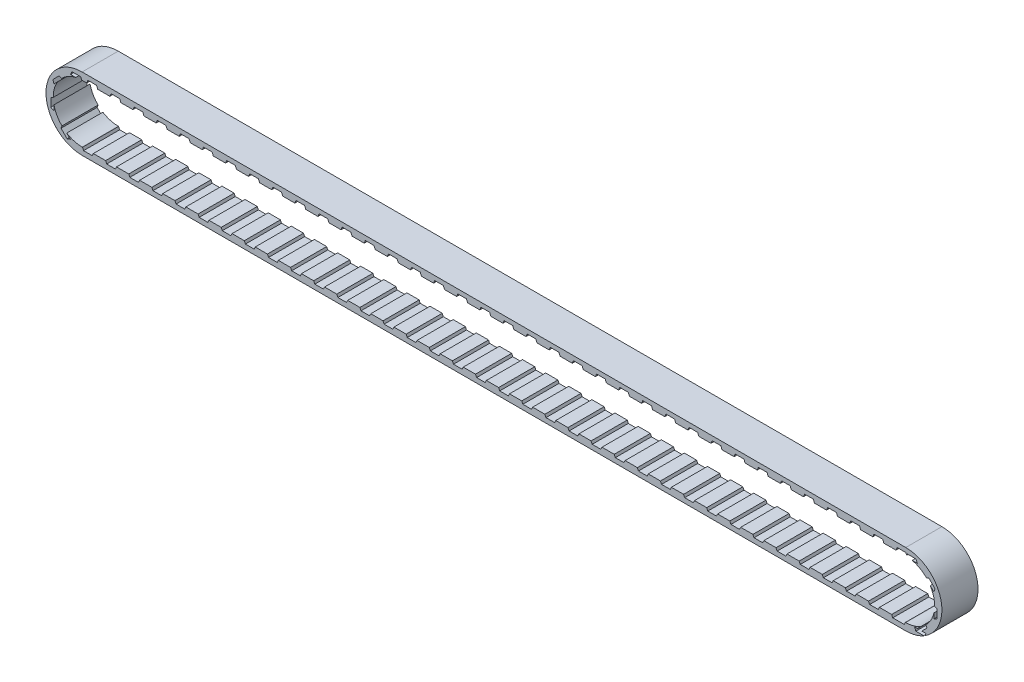
SolidWorks part; units mm, degrees
ref_plane "Front Plane" through (0, 0, 0) normal (0, 0, 1) x (1, 0, 0)
ref_plane "Top Plane" through (0, 0, 0) normal (0, 1, 0) x (1, 0, 0)
ref_plane "Right Plane" through (0, 0, 0) normal (1, 0, 0) x (0, 0, -1)
sketch "Sketch1" plane through (0, 0, 0) normal (0, 0, 1) x (1, 0, 0)
  line L1 (-72.39, 6.35) -> (72.39, 6.35)
  line L2 (-72.39, 5.08) -> (72.39, 5.08)
  line L3 (-72.39, -6.35) -> (72.39, -6.35)
  line L5 (-72.39, 6.35) -> (72.39, -6.35) construction
  line L6 (-72.39, -6.35) -> (72.39, 6.35) construction
  line L7 (-72.39, -5.08) -> (72.39, -5.08)
  line L9 (-72.39, 5.08) -> (72.39, -5.08) construction
  line L10 (-72.39, -5.08) -> (72.39, 5.08) construction
  arc A0 (-72.39, 6.35) -> (-72.39, -6.35) centre (-72.39, 0) ccw
  arc A1 (72.39, 6.35) -> (72.39, -6.35) centre (72.39, 0) cw
  arc A2 (-72.39, 5.08) -> (-72.39, -5.08) centre (-72.39, 0) ccw
  arc A3 (72.39, 5.08) -> (72.39, -5.08) centre (72.39, 0) cw
  point P0 (0, 0)
  point P8 (0, 0)
  point P15 (-78.74, 0)
  point P16 (78.74, 0)
  dimension "D2" = 6.35
  dimension "D4" = 144.78
  dimension "D1" = 144.78
  dimension "D3" = 1.27
  dimension "D5" = 144.78
extrude "Boss-Extrude1" add sketch "Sketch1" against normal blind 6.35
sketch "Sketch2" plane through (0, 0, 0) normal (0, 0, 1) x (1, 0, 0)
  line L0 (-72.39, -4.953) -> (-70.358, -4.953)
  line L3 (-70.358, -4.953) -> (-70.612, -5.5007)
  line L4 (-70.612, -5.5007) -> (-72.136, -5.5007)
  line L6 (-72.136, -5.5007) -> (-72.39, -4.953)
  line L7 (-72.39, -5.08) -> (72.39, -5.08) construction
  dimension "D1" = 0.127
  dimension "D2" = 1.524
  dimension "D3" = 2.032
  dimension "D4" = 0
extrude "Cut-Extrude1" cut sketch "Sketch2" against normal blind 8.89
pattern_linear "LPattern3" count 42 spacing 4.064 along (1, 0, 0) of "Cut-Extrude1"
pattern_circular "CirPattern1" count 8 over 360 about axis through (-72.39, 0, 0) along (0, 0, 1) of "Cut-Extrude1"
mirror "Mirror1" about plane through (0, 0, 0) normal (1, 0, 0) of "CirPattern1", "Cut-Extrude1"
sketch "Sketch3" plane through (0, 0, 0) normal (0, 0, 1) x (1, 0, 0)
  line L0 (-71.628, 4.953) -> (-69.596, 4.953)
  line L1 (-69.596, 4.953) -> (-69.85, 5.588)
  line L2 (-69.85, 5.588) -> (-71.374, 5.588)
  line L3 (-71.374, 5.588) -> (-71.628, 4.953)
  line L4 (72.39, 6.35) -> (-72.39, 6.35) construction
  dimension "D1" = 2.032
  dimension "D2" = 0.635
  dimension "D3" = 0.762
  dimension "D4" = 1.524
  dimension "D5" = 2.54
extrude "Cut-Extrude2" cut sketch "Sketch3" against normal blind 8.89
pattern_linear "LPattern2" count 36 spacing 4.064 along (1, 0, 0) of "Cut-Extrude2"
